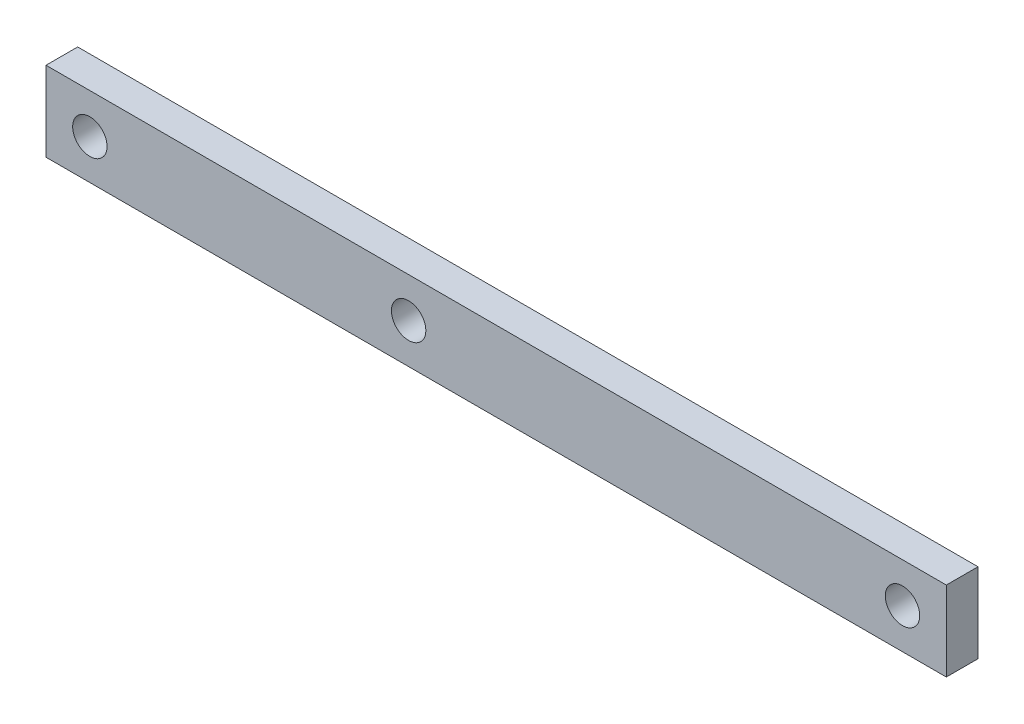
SolidWorks part; units mm, degrees
ref_plane "Front Plane" through (0, 0, 0) normal (0, 0, 1) x (1, 0, 0)
ref_plane "Top Plane" through (0, 0, 0) normal (0, 1, 0) x (1, 0, 0)
ref_plane "Right Plane" through (0, 0, 0) normal (1, 0, 0) x (0, 0, -1)
sketch "Sketch1" plane through (0, 0, 0) normal (0, 0, 1) x (1, 0, 0)
  line L1 (0, 0) -> (90.38, 0)
  line L2 (0, 0) -> (0, 8)
  line L3 (0, 8) -> (90.38, 8)
  line L4 (90.38, 0) -> (90.38, 8)
  dimension "D1" = 8
  dimension "D2" = 90.38
extrude "Boss-Extrude1" add sketch "Sketch1" along normal blind 3.18 contours L4 L3 L2 L1
sketch "Sketch2" plane through (0, 0, 3.18) normal (0, 0, 1) x (1, 0, 0)
  line L0 (0, 8) -> (90.38, 8) construction
  circle A0 centre (4.4024, 4) radius 1.7272
  dimension "D2" = 3.4544
  dimension "D1" = 4
extrude "Cut-Extrude1" cut sketch "Sketch2" against normal through all contours A0
pattern_linear "LPattern1" count 2 spacing 32 along (1, 0, 0) of "Cut-Extrude1"
pattern_linear "LPattern2" count 2 spacing 81.58 along (1, 0, 0) of "Cut-Extrude1"
equation "\"$\"= 1.6mm'SwindleClack"
equation "\"D1@Sketch1\"=\"$\" * 5"
equation "\"D1@Sketch2\"= 2.5 * \"$\""
equation "\"D3@LPattern1\"=\"$\" * 20"
equation "\"plate\"= \"$\" * 2'thickness of lego plate"
